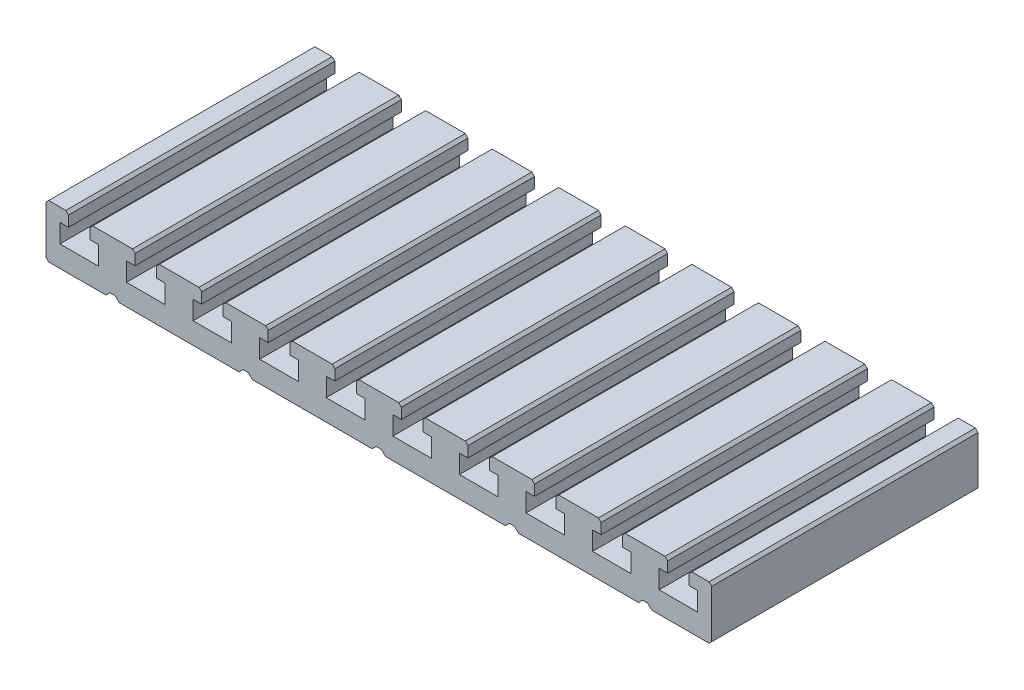
SolidWorks part; units mm, degrees
material "6063-T6"
ref_plane "Спереди" through (0, 0, 0) normal (0, 0, 1) x (1, 0, 0)
ref_plane "Сверху" through (0, 0, 0) normal (0, 1, 0) x (1, 0, 0)
ref_plane "Справа" through (0, 0, 0) normal (1, 0, 0) x (0, 0, -1)
sketch "Эскиз1" plane through (0, 0, 0) normal (0, 0, 1) x (1, 0, 0)
  point P4 (0, 0)
  line B0 (-52.5, 0) -> (-51, 1.5)
  line B1 (-51, 1.5) -> (-49, 1.5)
  line B2 (-49, 1.5) -> (-47.5, 0)
  line B3 (-47.5, 0) -> (-2.5, 0)
  line B4 (-2.5, 0) -> (-1, 1.5)
  line B5 (-1, 1.5) -> (1, 1.5)
  line B6 (1, 1.5) -> (2.5, 0)
  line B7 (2.5, 0) -> (47.5, 0)
  line B8 (47.5, 0) -> (49, 1.5)
  line B9 (49, 1.5) -> (51, 1.5)
  line B10 (51, 1.5) -> (52.5, 0)
  line B11 (52.5, 0) -> (97.5, 0)
  line B12 (97.5, 0) -> (99, 1.5)
  line B13 (99, 1.5) -> (101, 1.5)
  line B14 (101, 1.5) -> (102.5, 0)
  line B15 (102.5, 0) -> (124, 0)
  line B16 (124, 0) -> (125, 1)
  line B17 (125, 1) -> (125, 19)
  line B18 (125, 19) -> (124, 20)
  line B19 (124, 20) -> (117.55, 20)
  line B20 (117.55, 20) -> (116.55, 19)
  line B21 (116.55, 19) -> (116.55, 15)
  line B22 (116.55, 15) -> (119.75, 15)
  line B23 (119.75, 15) -> (119.75, 8)
  line B24 (119.75, 8) -> (105.25, 8)
  line B25 (105.25, 8) -> (105.25, 15)
  line B26 (105.25, 15) -> (108.45, 15)
  line B27 (108.45, 15) -> (108.45, 19)
  line B28 (108.45, 19) -> (107.45, 20)
  line B29 (107.45, 20) -> (92.55, 20)
  line B30 (92.55, 20) -> (91.55, 19)
  line B31 (91.55, 19) -> (91.55, 15)
  line B32 (91.55, 15) -> (94.75, 15)
  line B33 (94.75, 15) -> (94.75, 8)
  line B34 (94.75, 8) -> (80.25, 8)
  line B35 (80.25, 8) -> (80.25, 15)
  line B36 (80.25, 15) -> (83.45, 15)
  line B37 (83.45, 15) -> (83.45, 19)
  line B38 (83.45, 19) -> (82.45, 20)
  line B39 (82.45, 20) -> (67.55, 20)
  line B40 (67.55, 20) -> (66.55, 19)
  line B41 (66.55, 19) -> (66.55, 15)
  line B42 (66.55, 15) -> (69.75, 15)
  line B43 (69.75, 15) -> (69.75, 8)
  line B44 (69.75, 8) -> (55.25, 8)
  line B45 (55.25, 8) -> (55.25, 15)
  line B46 (55.25, 15) -> (58.45, 15)
  line B47 (58.45, 15) -> (58.45, 19)
  line B48 (58.45, 19) -> (57.45, 20)
  line B49 (57.45, 20) -> (42.55, 20)
  line B50 (42.55, 20) -> (41.55, 19)
  line B51 (41.55, 19) -> (41.55, 15)
  line B52 (41.55, 15) -> (44.75, 15)
  line B53 (44.75, 15) -> (44.75, 8)
  line B54 (44.75, 8) -> (30.25, 8)
  line B55 (30.25, 8) -> (30.25, 15)
  line B56 (30.25, 15) -> (33.45, 15)
  line B57 (33.45, 15) -> (33.45, 19)
  line B58 (33.45, 19) -> (32.45, 20)
  line B59 (32.45, 20) -> (17.55, 20)
  line B60 (17.55, 20) -> (16.55, 19)
  line B61 (16.55, 19) -> (16.55, 15)
  line B62 (16.55, 15) -> (19.75, 15)
  line B63 (19.75, 15) -> (19.75, 8)
  line B64 (19.75, 8) -> (5.25, 8)
  line B65 (5.25, 8) -> (5.25, 15)
  line B66 (5.25, 15) -> (8.45, 15)
  line B67 (8.45, 15) -> (8.45, 19)
  line B68 (8.45, 19) -> (7.45, 20)
  line B69 (7.45, 20) -> (-7.45, 20)
  line B70 (-7.45, 20) -> (-8.45, 19)
  line B71 (-8.45, 19) -> (-8.45, 15)
  line B72 (-8.45, 15) -> (-5.25, 15)
  line B73 (-5.25, 15) -> (-5.25, 8)
  line B74 (-5.25, 8) -> (-19.75, 8)
  line B75 (-19.75, 8) -> (-19.75, 15)
  line B76 (-19.75, 15) -> (-16.55, 15)
  line B77 (-16.55, 15) -> (-16.55, 19)
  line B78 (-16.55, 19) -> (-17.55, 20)
  line B79 (-17.55, 20) -> (-32.45, 20)
  line B80 (-32.45, 20) -> (-33.45, 19)
  line B81 (-33.45, 19) -> (-33.45, 15)
  line B82 (-33.45, 15) -> (-30.25, 15)
  line B83 (-30.25, 15) -> (-30.25, 8)
  line B84 (-30.25, 8) -> (-44.75, 8)
  line B85 (-44.75, 8) -> (-44.75, 15)
  line B86 (-44.75, 15) -> (-41.55, 15)
  line B87 (-41.55, 15) -> (-41.55, 19)
  line B88 (-41.55, 19) -> (-42.55, 20)
  line B89 (-42.55, 20) -> (-57.45, 20)
  line B90 (-57.45, 20) -> (-58.45, 19)
  line B91 (-58.45, 19) -> (-58.45, 15)
  line B92 (-58.45, 15) -> (-55.25, 15)
  line B93 (-55.25, 15) -> (-55.25, 8)
  line B94 (-55.25, 8) -> (-69.75, 8)
  line B95 (-69.75, 8) -> (-69.75, 15)
  line B96 (-69.75, 15) -> (-66.55, 15)
  line B97 (-66.55, 15) -> (-66.55, 19)
  line B98 (-66.55, 19) -> (-67.55, 20)
  line B99 (-67.55, 20) -> (-82.45, 20)
  line B100 (-82.45, 20) -> (-83.45, 19)
  line B101 (-83.45, 19) -> (-83.45, 15)
  line B102 (-83.45, 15) -> (-80.25, 15)
  line B103 (-80.25, 15) -> (-80.25, 8)
  line B104 (-80.25, 8) -> (-94.75, 8)
  line B105 (-94.75, 8) -> (-94.75, 15)
  line B106 (-94.75, 15) -> (-91.55, 15)
  line B107 (-91.55, 15) -> (-91.55, 19)
  line B108 (-91.55, 19) -> (-92.55, 20)
  line B109 (-92.55, 20) -> (-107.45, 20)
  line B110 (-107.45, 20) -> (-108.45, 19)
  line B111 (-108.45, 19) -> (-108.45, 15)
  line B112 (-108.45, 15) -> (-105.25, 15)
  line B113 (-105.25, 15) -> (-105.25, 8)
  line B114 (-105.25, 8) -> (-119.75, 8)
  line B115 (-119.75, 8) -> (-119.75, 15)
  line B116 (-119.75, 15) -> (-116.55, 15)
  line B117 (-116.55, 15) -> (-116.55, 19)
  line B118 (-116.55, 19) -> (-117.55, 20)
  line B119 (-117.55, 20) -> (-124, 20)
  line B120 (-124, 20) -> (-125, 19)
  line B121 (-125, 19) -> (-125, 1)
  line B122 (-125, 1) -> (-124, 0)
  line B123 (-124, 0) -> (-102.5, 0)
  line B124 (-102.5, 0) -> (-101, 1.5)
  line B125 (-101, 1.5) -> (-99, 1.5)
  line B126 (-99, 1.5) -> (-97.5, 0)
  line B127 (-97.5, 0) -> (-52.5, 0)
sketch_block_instance "Блок1-1"
sketch_block "Блок1"
extrude "Бобышка-Вытянуть1" add sketch "Эскиз1" against normal blind 100
